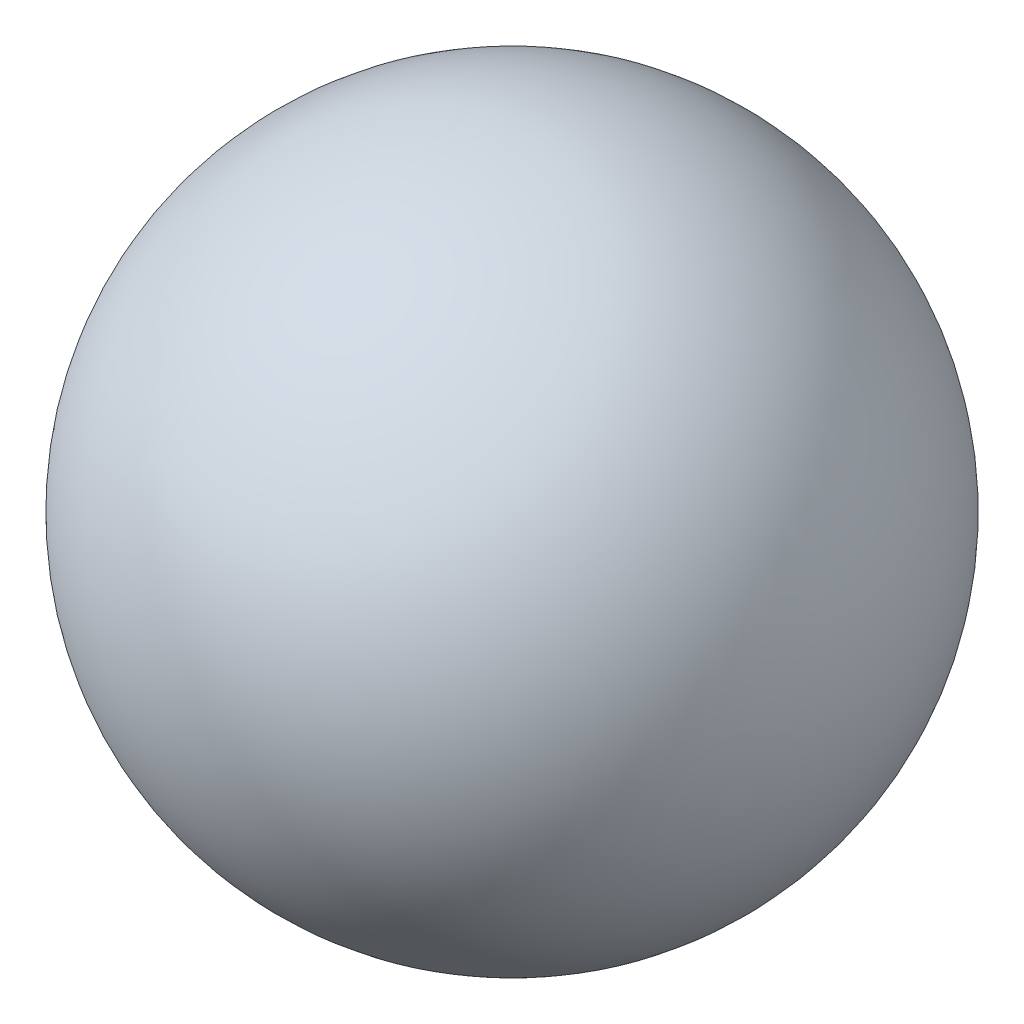
SolidWorks part; units mm, degrees
ref_plane "Front Plane" through (0, 0, 0) normal (0, 0, 1) x (1, 0, 0)
ref_plane "Top Plane" through (0, 0, 0) normal (0, 1, 0) x (1, 0, 0)
ref_plane "Right Plane" through (0, 0, 0) normal (1, 0, 0) x (0, 0, -1)
sketch "Sketch2" plane through (0, 0, 0) normal (0, 0, 1) x (1, 0, 0)
  line L0 (0, 150) -> (0, -150)
  arc A1 (0, 150) -> (0, -150) centre (0, 0) cw
  point P5 (0, 0)
revolve "Revolve1" add sketch "Sketch2" angle 360 about L0
sketch3d "3DSketch1"
  point P0 (0, 0, 0)
